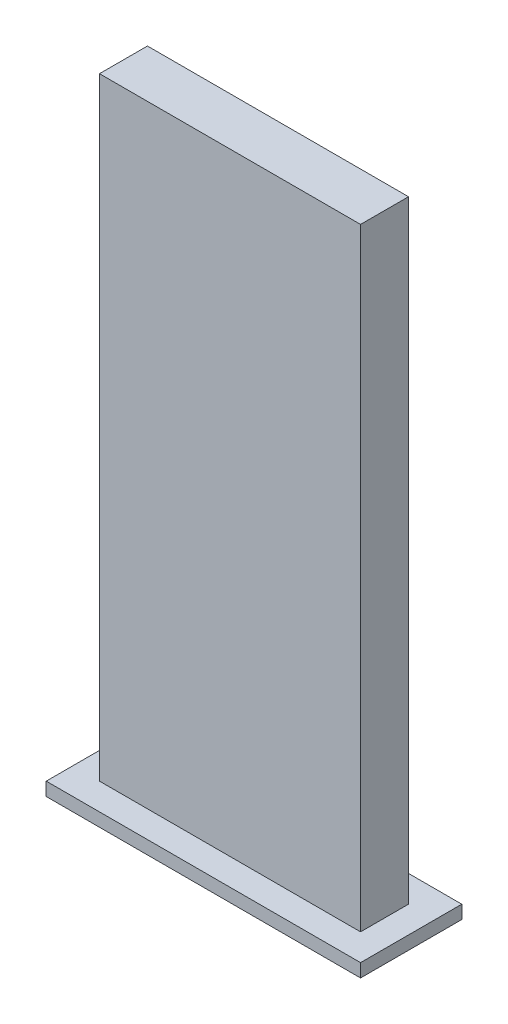
SolidWorks part; units mm, degrees
ref_plane "Front Plane" through (0, 0, 0) normal (0, 0, 1) x (1, 0, 0)
ref_plane "Top Plane" through (0, 0, 0) normal (0, 1, 0) x (1, 0, 0)
ref_plane "Right Plane" through (0, 0, 0) normal (1, 0, 0) x (0, 0, -1)
sketch "Sketch1" plane through (0, 0, 0) normal (0, 1, 0) x (1, 0, 0)
  line L1 (-5.9, 1.9) -> (5.9, 1.9)
  line L2 (-5.9, 1.9) -> (-5.9, -1.9)
  line L3 (-5.9, -1.9) -> (5.9, -1.9)
  line L4 (5.9, 1.9) -> (5.9, -1.9)
  line L5 (-5.9, 1.9) -> (5.9, -1.9) construction
  line L6 (-5.9, -1.9) -> (5.9, 1.9) construction
  point P0 (0, 0)
  dimension "D1" = 11.8
  dimension "D2" = 3.8
extrude "Boss-Extrude1" add sketch "Sketch1" along normal blind 0.5
sketch "Sketch2" plane through (0, 0.5, 0) normal (0, 1, 0) x (1, 0, 0)
  line L1 (-4.9, 0.9) -> (4.9, 0.9)
  line L2 (-4.9, 0.9) -> (-4.9, -0.9)
  line L3 (-4.9, -0.9) -> (4.9, -0.9)
  line L4 (4.9, 0.9) -> (4.9, -0.9)
  line L5 (-4.9, 0.9) -> (4.9, -0.9) construction
  line L6 (-4.9, -0.9) -> (4.9, 0.9) construction
  point P0 (0, 0)
  dimension "D1" = 9.8
  dimension "D2" = 1.8
extrude "Boss-Extrude2" add sketch "Sketch2" along normal blind 23
